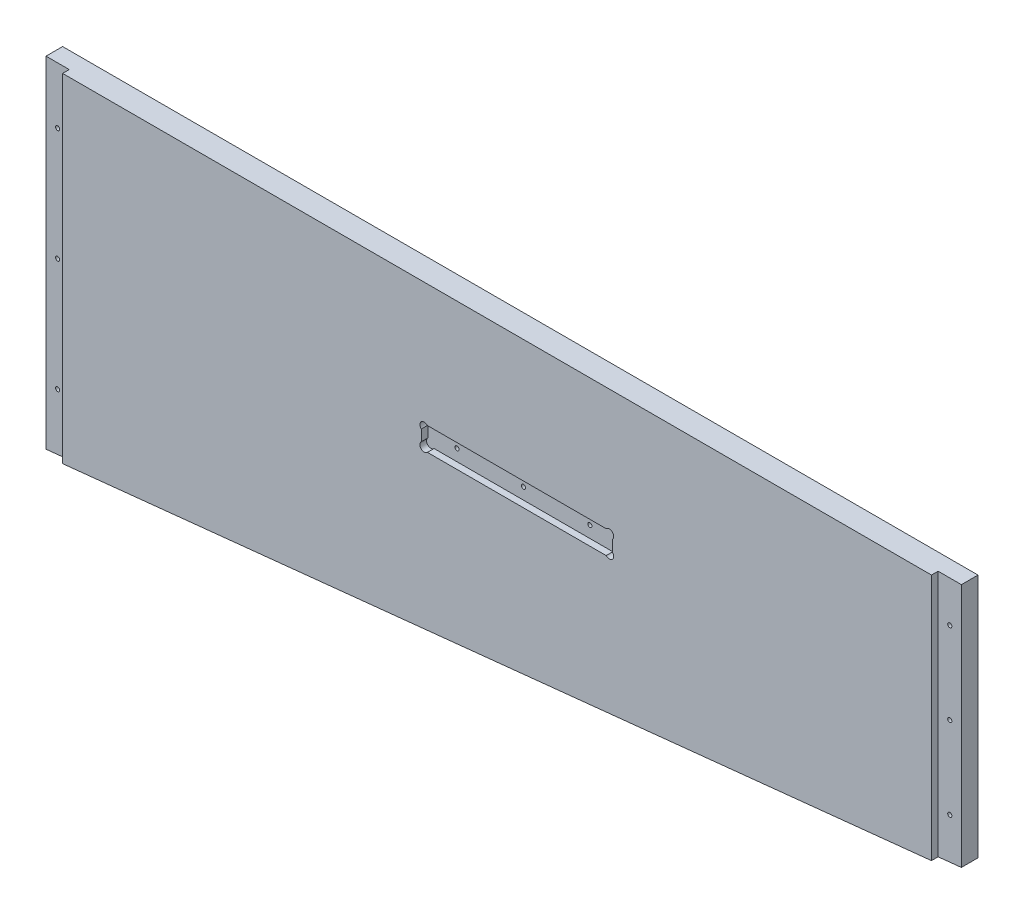
SolidWorks part; units mm, degrees
material "Pine"
ref_plane "Front Plane" through (0, 0, 0) normal (0, 0, 1) x (1, 0, 0)
ref_plane "Top Plane" through (0, 0, 0) normal (0, 1, 0) x (1, 0, 0)
ref_plane "Right Plane" through (0, 0, 0) normal (1, 0, 0) x (0, 0, -1)
sketch "Sketch1" plane through (0, 0, 0) normal (0, 0, 1) x (1, 0, 0)
  line L0 (-163.9887, -5335.905) -> (-163.9887, -5432.425)
  line L1 (-102.87, -5350.891) -> (-33.02, -5350.891)
  line L2 (-111.8235, -5341.9375) -> (-111.8235, -5334)
  line L3 (-24.0665, -5341.9375) -> (-24.0665, -5334)
  line L4 (-298.9262, -5332.73) -> (-167.1637, -5332.73)
  line L5 (-167.1637, -5435.6) -> (-298.9262, -5435.6)
  line L6 (-302.1012, -5432.425) -> (-302.1012, -5335.905)
  line L7 (-107.6325, -5329.809) -> (-28.2575, -5329.809)
  line L8 (174.9425, -5308.6) -> (174.9425, -5581.65)
  line L9 (449.2625, -5413.1661) -> (449.2625, -5421.9659)
  line L10 (595.3125, -5421.9659) -> (595.3125, -5413.1661)
  line L11 (839.47, -5509.5521) -> (839.47, -5307.6729)
  line L12 (839.47, -5307.6729) -> (863.6, -5307.6729)
  line L13 (839.47, -5509.5521) -> (863.6, -5509.5521)
  line L14 (863.6, -5509.5521) -> (863.6, -5307.6729)
  line L15 (-354.2665, -5341.9375) -> (-354.2665, -5334)
  line L16 (-100.8856, -5889.625) -> (-50.0856, -5889.625)
  line L17 (-104.0606, -5969) -> (-104.0606, -5892.8)
  line L18 (-46.9106, -5892.8) -> (-46.9106, -5969)
  line L19 (-50.0856, -5972.175) -> (-100.8856, -5972.175)
  line L20 (-100.8856, -5848.35) -> (-50.0856, -5848.35)
  line L21 (857.25, -5502.275) -> (157.1625, -5575.3)
  line L22 (857.25, -5314.95) -> (857.25, -5502.275)
  line L23 (157.1625, -5314.95) -> (157.1625, -5575.3)
  line L24 (857.25, -5314.95) -> (157.1625, -5314.95)
  line L25 (150.8125, -5308.6) -> (174.9425, -5308.6)
  line L26 (174.9425, -5581.65) -> (150.8125, -5581.65)
  line L27 (137.16, -5314.95) -> (137.16, -5502.275)
  line L28 (150.8125, -5581.65) -> (150.8125, -5308.6)
  line L29 (590.8224, -5408.676) -> (453.7526, -5408.676)
  line L30 (453.7526, -5426.456) -> (590.8224, -5426.456)
  line L31 (137.16, -6013.45) -> (137.16, -5867.4)
  line L32 (150.8125, -5746.75) -> (150.8125, -6019.8)
  line L33 (143.51, -5639.9938) -> (143.51, -5654.294)
  line L34 (590.8224, -5919.724) -> (453.7526, -5919.724)
  line L35 (453.7526, -5901.944) -> (590.8224, -5901.944)
  line L36 (449.2625, -5915.2339) -> (449.2625, -5906.4341)
  line L37 (174.9425, -6019.8) -> (174.9425, -5746.75)
  line L38 (595.3125, -5906.4341) -> (595.3125, -5915.2339)
  line L39 (839.47, -5818.8479) -> (839.47, -6020.7271)
  line L40 (839.47, -5818.8479) -> (863.6, -5818.8479)
  line L41 (863.6, -5818.8479) -> (863.6, -6020.7271)
  line L42 (839.47, -6020.7271) -> (863.6, -6020.7271)
  line L43 (-155.8782, -5867.4) -> (-603.25, -5867.4)
  line L44 (-433.07, -5350.891) -> (-363.22, -5350.891)
  line L45 (-437.8325, -5329.809) -> (-358.4575, -5329.809)
  line L46 (889, -6045.2) -> (-635, -6045.2)
  line L47 (-635, -5283.2) -> (889, -5283.2)
  line L48 (-635, -6045.2) -> (-635, -5283.2)
  line L49 (889, -5283.2) -> (889, -6045.2)
  line L50 (137.16, -5502.275) -> (-603.25, -5502.275)
  line L51 (-603.25, -5314.95) -> (137.16, -5314.95)
  line L52 (143.51, -5654.294) -> (-609.6, -5654.294)
  line L53 (-609.6, -5639.9938) -> (143.51, -5639.9938)
  line L54 (137.16, -5536.0062) -> (-603.25, -5536.0062)
  line L55 (-603.25, -5794.375) -> (137.16, -5794.375)
  line L56 (-603.25, -6013.45) -> (137.16, -6013.45)
  line L57 (-603.25, -5536.0062) -> (-603.25, -5794.375)
  line L58 (137.16, -5794.375) -> (137.16, -5536.0062)
  line L59 (-609.6, -5654.294) -> (-609.6, -5639.9938)
  line L60 (-603.25, -5867.4) -> (-603.25, -6013.45)
  line L61 (-603.25, -5314.95) -> (-603.25, -5502.275)
  line L62 (-442.0235, -5341.9375) -> (-442.0235, -5334)
  line L63 (857.25, -5826.125) -> (157.1625, -5753.1)
  line L64 (857.25, -6013.45) -> (857.25, -5826.125)
  line L65 (157.1625, -6013.45) -> (157.1625, -5753.1)
  line L66 (857.25, -6013.45) -> (157.1625, -6013.45)
  line L67 (174.9425, -5746.75) -> (150.8125, -5746.75)
  line L68 (150.8125, -6019.8) -> (174.9425, -6019.8)
  line L69 (137.16, -5867.4) -> (4.907, -5867.4)
  circle A0 centre (-36.195, -5484.0124) radius 1.5875
  arc A1 (-298.9262, -5332.73) -> (-302.1012, -5335.905) centre (-298.9262, -5335.905) ccw
  arc A2 (-302.1012, -5432.425) -> (-298.9262, -5435.6) centre (-298.9262, -5432.425) ccw
  arc A3 (-163.9887, -5335.905) -> (-167.1637, -5332.73) centre (-167.1637, -5335.905) ccw
  arc A4 (-167.1637, -5435.6) -> (-163.9887, -5432.425) centre (-167.1637, -5432.425) ccw
  arc A5 (-111.8235, -5341.9375) -> (-102.87, -5350.891) centre (-102.87, -5341.9375) ccw
  arc A6 (-107.6325, -5329.809) -> (-111.8235, -5334) centre (-107.6325, -5334) ccw
  circle A7 centre (166.0525, -5444.6613) radius 1.5875
  circle A8 centre (166.0525, -5358.1871) radius 1.5875
  circle A9 centre (471.4875, -5417.566) radius 1.5875
  arc A10 (453.7526, -5408.676) -> (449.2625, -5413.1661) centre (451.5076, -5410.9211) ccw
  arc A11 (449.2625, -5421.9659) -> (453.7526, -5426.456) centre (451.5076, -5424.2109) ccw
  circle A12 centre (522.2875, -5417.566) radius 1.5875
  circle A13 centre (573.0875, -5417.566) radius 1.5875
  arc A14 (590.8224, -5426.456) -> (595.3125, -5421.9659) centre (593.0674, -5424.2109) ccw
  arc A15 (595.3125, -5413.1661) -> (590.8224, -5408.676) centre (593.0674, -5410.9211) ccw
  circle A16 centre (848.36, -5471.8269) radius 1.5875
  circle A17 centre (848.36, -5409.0762) radius 1.5875
  circle A18 centre (848.36, -5346.3254) radius 1.5875
  arc A19 (-363.22, -5350.891) -> (-354.2665, -5341.9375) centre (-363.22, -5341.9375) ccw
  arc A20 (-354.2665, -5334) -> (-358.4575, -5329.809) centre (-358.4575, -5334) ccw
  arc A21 (-24.0665, -5334) -> (-28.2575, -5329.809) centre (-28.2575, -5334) ccw
  arc A22 (-33.02, -5350.891) -> (-24.0665, -5341.9375) centre (-33.02, -5341.9375) ccw
  circle A23 centre (-86.995, -5484.0124) radius 1.5875
  circle A24 centre (-333.4544, -5894.07) radius 2.54
  circle A25 centre (-333.4544, -5994.4) radius 2.54
  arc A26 (-104.0606, -5969) -> (-100.8856, -5972.175) centre (-100.8856, -5969) ccw
  arc A27 (-50.0856, -5972.175) -> (-46.9106, -5969) centre (-50.0856, -5969) ccw
  arc A28 (-100.8856, -5848.35) -> (-128.3819, -5857.875) centre (-100.8856, -5892.8) ccw
  arc A29 (-155.8782, -5867.4) -> (-128.3819, -5857.875) centre (-155.8782, -5822.95) ccw
  arc A30 (-22.5893, -5857.875) -> (-50.0856, -5848.35) centre (-50.0856, -5892.8) ccw
  circle A31 centre (-132.6356, -5894.07) radius 2.54
  circle A32 centre (-132.6356, -5994.4) radius 2.54
  arc A33 (-46.9106, -5892.8) -> (-50.0856, -5889.625) centre (-50.0856, -5892.8) ccw
  arc A34 (-100.8856, -5889.625) -> (-104.0606, -5892.8) centre (-100.8856, -5892.8) ccw
  arc A35 (-22.5893, -5857.875) -> (4.907, -5867.4) centre (4.907, -5822.95) ccw
  circle A36 centre (166.0525, -5531.1356) radius 1.5875
  arc A37 (449.2625, -5915.2339) -> (453.7526, -5919.724) centre (451.5076, -5917.4789) ccw
  arc A38 (453.7526, -5901.944) -> (449.2625, -5906.4341) centre (451.5076, -5904.1891) ccw
  circle A39 centre (166.0525, -5797.2644) radius 1.5875
  circle A40 centre (166.0525, -5883.7387) radius 1.5875
  circle A41 centre (166.0525, -5970.2129) radius 1.5875
  circle A42 centre (471.4875, -5910.834) radius 1.5875
  circle A43 centre (522.2875, -5910.834) radius 1.5875
  circle A44 centre (573.0875, -5910.834) radius 1.5875
  arc A45 (595.3125, -5906.4341) -> (590.8224, -5901.944) centre (593.0674, -5904.1891) ccw
  arc A46 (590.8224, -5919.724) -> (595.3125, -5915.2339) centre (593.0674, -5917.4789) ccw
  circle A47 centre (848.36, -5919.3238) radius 1.5875
  circle A48 centre (848.36, -5982.0746) radius 1.5875
  circle A49 centre (848.36, -5856.5731) radius 1.5875
  arc A50 (-437.8325, -5329.809) -> (-442.0235, -5334) centre (-437.8325, -5334) ccw
  circle A51 centre (-429.895, -5484.0124) radius 1.5875
  arc A52 (-442.0235, -5341.9375) -> (-433.07, -5350.891) centre (-433.07, -5341.9375) ccw
  circle A53 centre (-379.095, -5484.0124) radius 1.5875
sketch "HeadSideLeftOutline" plane through (0, 0, 0) normal (0, 0, 1) x (1, 0, 0)
  line L0 (839.47, -5504.1296) -> (839.47, -5314.95)
  line L1 (839.47, -5314.95) -> (174.9425, -5314.95)
  line L2 (174.9425, -5314.95) -> (174.9425, -5573.4454)
  line L3 (174.9425, -5573.4454) -> (839.47, -5504.1296)
  line L4 (174.9425, -5308.6) -> (174.9425, -5581.65) construction
  line L5 (857.25, -5314.95) -> (157.1625, -5314.95) construction
  line L6 (839.47, -5509.5521) -> (839.47, -5307.6729) construction
extrude "HeadSideLeft_Thickness" add sketch "HeadSideLeftOutline" against normal blind 17.78
sketch "HeadSideLeftLedge" plane through (0, 0, -17.78) normal (0, 0, -1) x (-1, 0, 0)
  line L0 (-174.9425, -5314.95) -> (-157.1625, -5314.95)
  line L1 (-157.1625, -5314.95) -> (-157.1625, -5575.3)
  line L2 (-157.1625, -5575.3) -> (-174.9425, -5573.4454)
  line L3 (-174.9425, -5573.4454) -> (-174.9425, -5314.95)
  line L4 (-839.47, -5314.95) -> (-857.25, -5314.95)
  line L5 (-857.25, -5314.95) -> (-857.25, -5502.275)
  line L6 (-857.25, -5502.275) -> (-839.47, -5504.1296)
  line L7 (-839.47, -5504.1296) -> (-839.47, -5314.95)
  line L8 (-857.25, -5502.275) -> (-157.1625, -5575.3) construction
  dimension "D1" = 17.78
  dimension "D2" = 17.78
extrude "HeadSideLeftLedge_Thickness" add sketch "HeadSideLeftLedge" against normal blind 12.7
sketch "Sketch4" plane through (0, 0, 0) normal (0, 0, 1) x (1, 0, 0)
  line L12 (449.2625, -5426.456) -> (595.3125, -5426.456)
  line L13 (595.3125, -5408.676) -> (595.3125, -5426.456)
  line L14 (595.3125, -5408.676) -> (449.2625, -5408.676)
  line L15 (449.2625, -5408.676) -> (449.2625, -5426.456)
  dimension "D1" = 17.78
extrude "Cut-Extrude2" cut sketch "Sketch4" against normal blind 5.08
sketch "Sketch6" plane through (0, 0, 0) normal (0, 0, 1) x (1, 0, 0)
  line L0 (595.3125, -5426.456) -> (593.0674, -5424.2109) construction
  line L1 (595.3125, -5408.676) -> (593.0674, -5410.9211) construction
  line L2 (449.2625, -5426.456) -> (451.5076, -5424.2109) construction
  line L3 (449.2625, -5408.676) -> (451.5076, -5410.9211) construction
  line L4 (449.2625, -5426.456) -> (595.3125, -5426.456) construction
  line L5 (595.3125, -5408.676) -> (449.2625, -5408.676) construction
  line L6 (449.2625, -5426.456) -> (595.3125, -5426.456) construction
  circle A0 centre (451.5076, -5410.9211) radius 3.302
  circle A1 centre (451.5076, -5424.2109) radius 3.302
  circle A2 centre (593.0674, -5424.2109) radius 3.302
  circle A3 centre (593.0674, -5410.9211) radius 3.302
  dimension "D1" = 45
  dimension "D2" = 45
  dimension "D3" = 3.175
  dimension "D4" = 3.175
  dimension "D5" = 45
  dimension "D6" = 45
  dimension "D7" = 3.175
  dimension "D8" = 3.175
extrude "Cut-Extrude3" cut sketch "Sketch6" against normal up to surface (5.08 mm away) up to face at (522.2875, -5417.566, -5.08)
sketch "Sketch3" plane through (0, 0, 0) normal (0, 0, 1) x (1, 0, 0)
  circle A0 centre (166.0525, -5531.1356) radius 1.5875
  circle A1 centre (166.0525, -5444.6613) radius 1.5875
  circle A2 centre (166.0525, -5358.1871) radius 1.5875
  circle A3 centre (848.36, -5471.8269) radius 1.5875
  circle A4 centre (848.36, -5409.0762) radius 1.5875
  circle A5 centre (848.36, -5346.3254) radius 1.5875
  circle A6 centre (573.0875, -5417.566) radius 1.5875
  circle A7 centre (522.2875, -5417.566) radius 1.5875
  circle A8 centre (471.4875, -5417.566) radius 1.5875
extrude "Cut-Extrude1" cut sketch "Sketch3" against normal up to surface (17.78 mm away) up to face at (507.2062, -5426.8687, -17.78)
